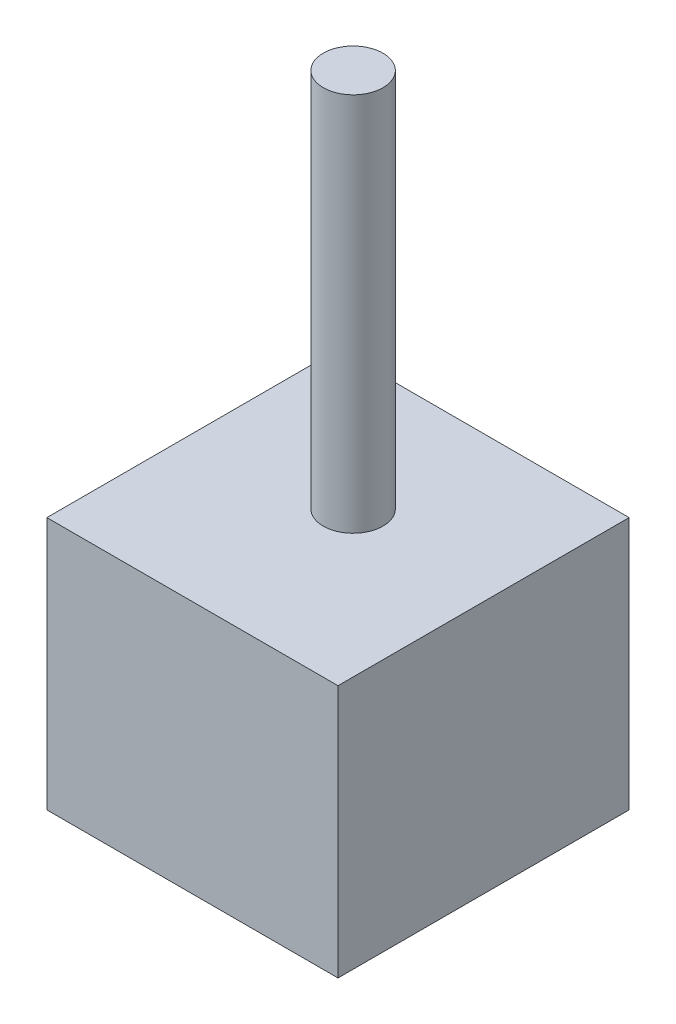
SolidWorks part; units mm, degrees
ref_plane "Front Plane" through (0, 0, 0) normal (0, 0, 1) x (1, 0, 0)
ref_plane "Top Plane" through (0, 0, 0) normal (0, 1, 0) x (1, 0, 0)
ref_plane "Right Plane" through (0, 0, 0) normal (1, 0, 0) x (0, 0, -1)
sketch "Sketch1" plane through (0, 0, 0) normal (0, 1, 0) x (1, 0, 0)
  line L1 (-29.21, -32.2402) -> (29.21, -32.2402)
  line L2 (-29.21, -32.2402) -> (-29.21, 26.1798)
  line L3 (-29.21, 26.1798) -> (29.21, 26.1798)
  line L4 (29.21, -32.2402) -> (29.21, 26.1798)
  point P4 (0, 26.1798)
  dimension "D1" = 58.42
  dimension "D2" = 58.42
extrude "Boss-Extrude1" add sketch "Sketch1" along normal blind 50.8
sketch "Sketch2" plane through (0, 50.8, 0) normal (0, 1, 0) x (1, 0, 0)
  circle A0 centre (0, 0) radius 6
  dimension "D1" = 12
extrude "Boss-Extrude2" add sketch "Sketch2" along normal blind 76.2
